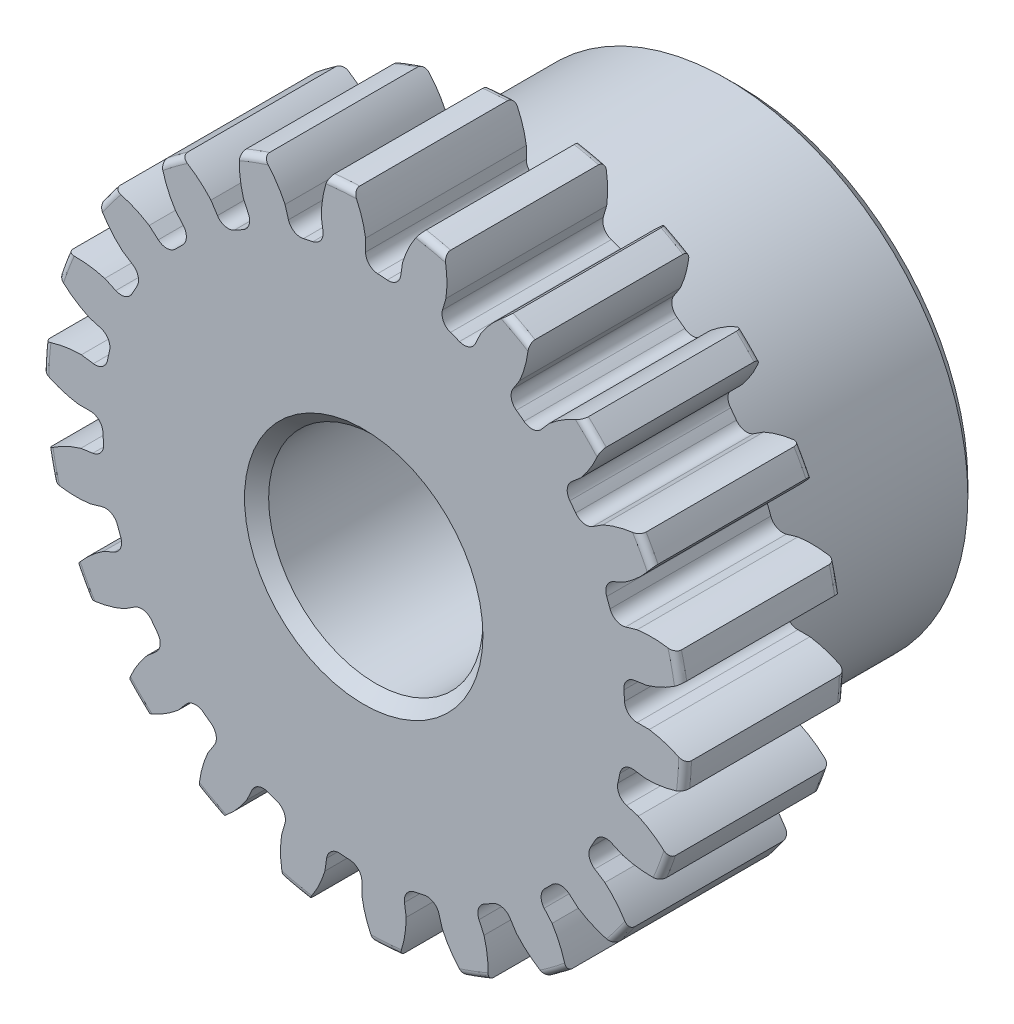
SolidWorks part; units mm, degrees
ref_plane "Front" through (0, 0, 0) normal (0, 0, 1) x (1, 0, 0)
ref_plane "Top" through (0, 0, 0) normal (0, 1, 0) x (1, 0, 0)
ref_plane "Right" through (0, 0, 0) normal (1, 0, 0) x (0, 0, -1)
sketch "Sketch1" plane through (0, 0, 0) normal (0, 0, 1) x (1, 0, 0)
  line L0 (-279.4, 0) -> (279.4, 0) construction
  circle A0 centre (0, 0) radius 9.525
  circle A1 centre (0, 0) radius 8.7376 construction
  circle A3 centre (0, 0) radius 7.7378 construction
  dimension "D1" = 1.7872
  dimension "OD" = 19.05
  dimension "Ptich Dia" = 17.4752
  dimension "Root Dia" = 15.4755
  dimension "D3" = 0.7874
  dimension "Number of Teeth" = 558.8
extrude "Boss-Extrude1" add sketch "Sketch1" against normal blind 4.7625
sketch "Sketch2" plane through (0, 0, 0) normal (1, 0, 0) x (0, 0, -1)
  line L0 (4.7625, 0) -> (11.1125, 0)
  line L1 (4.7625, 0) -> (4.7625, 7.1438)
  line L2 (4.7625, 7.1438) -> (11.1125, 7.1437)
  line L3 (11.1125, 7.1437) -> (11.1125, 0)
  point P5 (11.1125, -7.1437)
  point P6 (0, -9.525)
  point P7 (4.7625, -9.525)
  point P9 (0, 9.525)
  dimension "Face Wd" = 4.7625
  dimension "B Hub Dia" = 14.2875
  dimension "D O'all Lg." = 11.1125
revolve "Revolve1" add sketch "Sketch2" angle 360 about L0
fillet "Fillet2" radius 0.1905 3 edges at (9.525, 0, -4.7625) (9.525, 0, 0) (7.1438, 0, -4.7625)
sketch "Sketch3" plane through (0, 0, 0) normal (0, 0, 1) x (1, 0, 0)
  line L0 (0, 0) -> (0, 9.525) construction
  line L1 (-2.118, 8.1898) -> (0, 8.7376)
  line L2 (-9.5921, 8.7376) -> (9.5921, 8.7376) construction
  line L3 (-9.2865, 6.3359) -> (9.2865, 11.1393) construction
  line L4 (-2.118, 8.1898) -> (0, 0) construction
  line L5 (-5.4024, 6.5095) -> (0, 0) construction
  line L6 (-5.4024, 6.5095) -> (-0.8766, 10.2656) construction
  line L7 (-1.4769, 8.3294) -> (0, 0) construction
  line L8 (-1.4769, 8.3294) -> (0.031, 8.5967) construction
  arc A0 (-2.118, 8.1898) -> (-5.4024, 6.5095) centre (0, 0) ccw
  circle A1 centre (0, 0) radius 8.7376 construction
  circle A2 centre (0, 0) radius 8.4593 construction
  arc A3 (-2.118, 8.1898) -> (-1.4769, 8.3294) centre (0, 0) cw
  circle A4 centre (0, 0) radius 9.525 construction
  point P6 (0, 8.7376)
  dimension "D1" = 2.1877
  dimension "Pressure Angle" = 14.5
  dimension "D2" = 3.7191
  dimension "D3" = 5.8814
  dimension "D4" = 0.6563
  dimension "D5" = 1.5314
sketch "Sketch4" plane through (0, 0, 0) normal (0, 0, 1) x (1, 0, 0)
  line L0 (0, 0) -> (0.6217, 8.6931) construction
  line L1 (0.0548, 8.4591) -> (0.0548, 7.7376)
  line L2 (0, 8.7376) -> (1.2435, 8.6487) construction
  line L3 (1.1496, 8.3808) -> (1.0469, 7.6666)
  line L4 (0.0548, 7.7376) -> (0, 0) construction
  line L5 (0, 0) -> (0, 9.525) construction
  line L6 (-5.4024, 6.5095) -> (-0.8766, 10.2656) construction
  line L7 (-5.4024, 6.5095) -> (-0.8766, 10.2656) construction
  arc A0 (1.0469, 7.6666) -> (0.0548, 7.7376) centre (0, 0) ccw
  arc A1 (0, 8.7376) -> (1.2435, 8.6487) centre (0, 0) cw construction
  circle A2 centre (0, 0) radius 8.7376 construction
  circle A3 centre (0, 0) radius 8.4593 construction
  circle A4 centre (0, 0) radius 7.7378 construction
  arc A5 (2.3286, 10.0364) -> (-0.8766, 10.2656) centre (0, 0) ccw
  spline S0 degree 2 poles (-0.8766, 10.2656) (-0.0977, 9.4713) (0.0548, 8.4591) knots 0 0 0 1 1 1
  spline S1 degree 2 poles (2.3286, 10.0364) (1.4446, 9.361) (1.1496, 8.3808) knots 0 0 0 1 1 1
  dimension "D1" = 1.2477
extrude "Cut-Extrude1" cut sketch "Sketch4" against normal through all
fillet "Fillet1" radius 0.3743 2 edges at (1.0469, 7.6666, -2.3813) (0.0548, 7.7376, -2.3813)
pattern_circular "CirPattern1" count 22 over 360 about axis through (0, 0, -4.7625) along (0, 0, 1) of "Cut-Extrude1", "Fillet1"
sketch "Sketch5" plane through (0, 0, 0) normal (0, 0, 1) x (1, 0, 0)
  circle A0 centre (0, 0) radius 3.175
  circle A1 centre (0, 0) radius 1.5875 construction
  dimension "Bore Min" = 6.35
  dimension "Bore Max" = 3.175
extrude "Cut-Extrude2" cut sketch "Sketch5" against normal through all
chamfer "Chamfer1" distance 0.3572 angle 45 3 edges at (7.1437, 0, -11.1125) (3.175, 0, 0) (3.175, 0, -11.1125)
sketch "Pitch Dia" plane through (0, 0, 0) normal (0, 0, 1) x (1, 0, 0)
  circle A0 centre (0, 0) radius 8.7376 construction
  circle A1 centre (0, 0) radius 8.7376 construction
equation "\"D1@Boss-Extrude1\" = \"Face Wd@Sketch2\""
equation "\"D2@Sketch3\" = \"D1@Sketch3\"*1.7"
equation "\"D3@Sketch3\" = \"D1@Sketch3\"+\"D2@Sketch3\"-.001"
equation "\"D4@Sketch3\" = \"D1@Sketch3\"*.3"
equation "\"D5@Sketch3\" = \"D1@Sketch3\"-\"D4@Sketch3\""
equation "\"D1@Sketch4\" = 1.5708/(\"Number of Teeth@Sketch1\"/\"Ptich Dia@Sketch1\")"
equation "\"D1@Chamfer1\" = \"B Hub Dia@Sketch2\"*.025"
equation "\"D1@CirPattern1\" = \"Number of Teeth@Sketch1\""
equation "\"D1@Fillet1\" = \"D1@Sketch4\"*.3"
equation "\"D1@Fillet2\" = \"OD@Sketch1\"*.01"
equation "\"D1@Sketch1\" = 2.250/(\"Number of Teeth@Sketch1\"/\"Ptich Dia@Sketch1\")"
